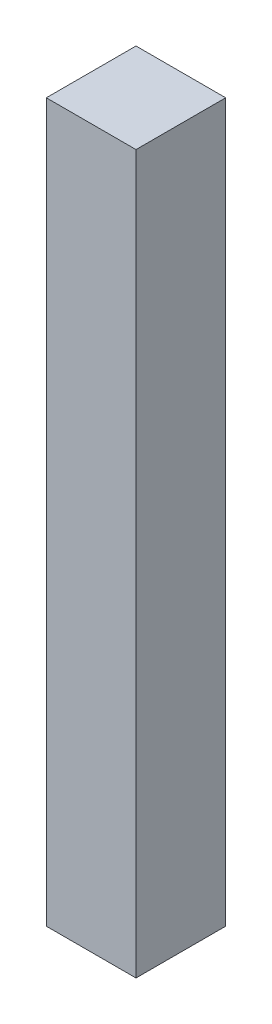
SolidWorks part; units mm, degrees
material "Beech"
ref_plane "Plane1" through (0, 0, 0) normal (0, 0, 1) x (1, 0, 0)
ref_plane "Plane2" through (0, 0, 0) normal (0, 1, 0) x (1, 0, 0)
ref_plane "Plane3" through (0, 0, 0) normal (1, 0, 0) x (0, 0, -1)
sketch "Sketch1" plane through (0, 0, 0) normal (0, 1, 0) x (1, 0, 0)
  line L1 (0, 0) -> (50, 0)
  line L2 (0, 0) -> (0, 50)
  line L3 (0, 50) -> (50, 50)
  line L4 (50, 0) -> (50, 50)
  dimension "D1" = 50
  dimension "D2" = 50
extrude "Boss-Extrude1" add sketch "Sketch1" along normal blind 400
